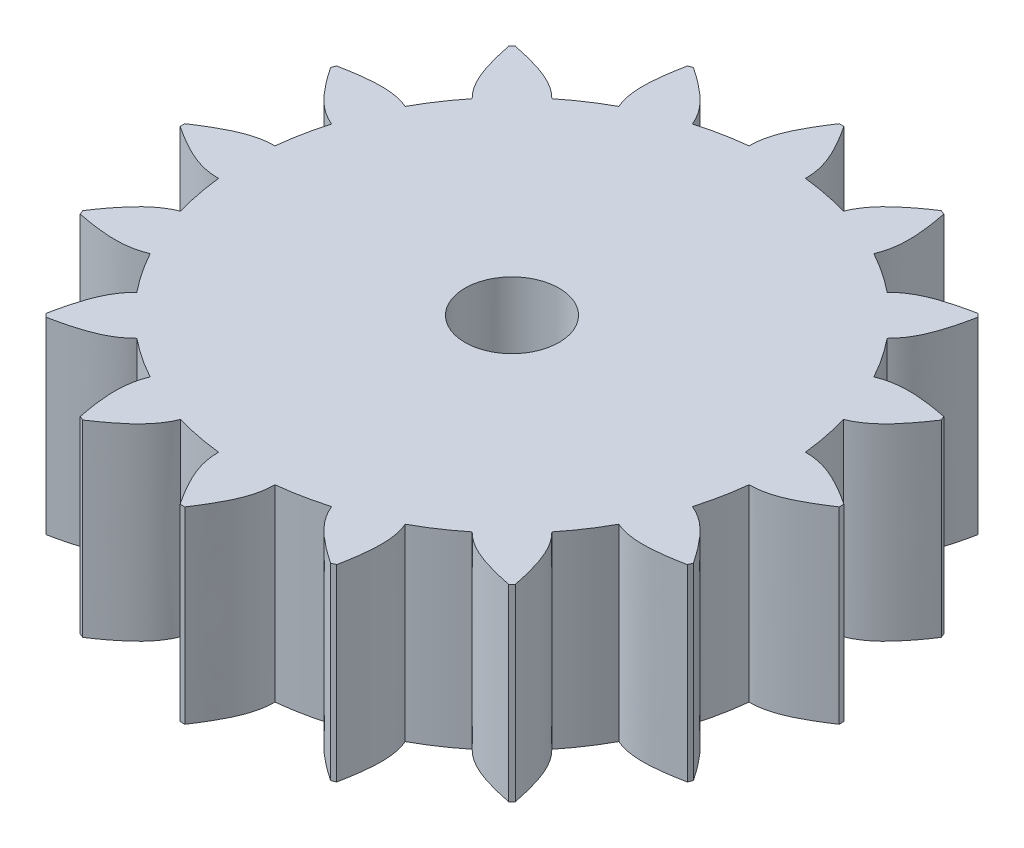
SolidWorks part; units mm, degrees
ref_plane "Front Plane" through (0, 0, 0) normal (0, 0, 1) x (1, 0, 0)
ref_plane "Top Plane" through (0, 0, 0) normal (0, 1, 0) x (1, 0, 0)
ref_plane "Right Plane" through (0, 0, 0) normal (1, 0, 0) x (0, 0, -1)
sketch "Sketch1" plane through (0, 0, 0) normal (0, 1, 0) x (1, 0, 0)
  line L0 (0, 0) -> (0, 10.795) construction
  line L1 (0, 0) -> (-1.3932, 10.7047) construction
  line L2 (0, 0) -> (1.3931, 10.7047) construction
  line L3 (0, 0) -> (4.0866, 9.9916) construction
  line L4 (0, 0) -> (6.5079, 8.6128) construction
  line L10 (1.3931, 10.7047) -> (-1.3776, 11.0653) construction
  line L11 (4.0866, 9.9916) -> (-1.0855, 12.107) construction
  line L12 (6.5079, 8.6128) -> (-0.1797, 13.6659) construction
  circle A0 centre (0, 0) radius 13.335
  circle A1 centre (0, 0) radius 10.795
  spline S0 degree 3 poles (-1.3932, 10.7047) (-1.4212, 11.7939) (-0.7474, 12.8124) (-0.1797, 13.6659) knots 0 0 0 0 1 1 1 1 construction
  spline S1 degree 3 poles (1.3932, 10.7047) (1.4212, 11.7939) (0.7474, 12.8124) (0.1797, 13.6659) knots 0 0 0 0 1 1 1 1 construction
  spline S2 degree 1 poles (-1.1392, 10.7113) (0.0318, 13.5253) knots 0 0 1 1 construction
  spline S3 degree 3 poles (-1.1392, 10.7113) (-1.1521, 11.2102) (-0.8543, 12.1818) (-0.2607, 13.0855) (0.0318, 13.5253) knots 0 0 0 0 0.5 1 1 1 1
  spline S4 degree 1 poles (1.1392, 10.7113) (-0.0318, 13.5253) knots 0 0 1 1 construction
  spline S5 degree 3 poles (1.1392, 10.7113) (1.1521, 11.2102) (0.8543, 12.1818) (0.2607, 13.0855) (-0.0318, 13.5253) knots 0 0 0 0 0.5 1 1 1 1
  dimension "D1" = 26.67
  dimension "D2" = 21.59
  dimension "D3" = 2.794
  dimension "D4" = 7.415
  dimension "D6" = 8.382
  dimension "D7" = 29.66
  dimension "D8" = 44.49
  dimension "D9" = 2.794
  dimension "D10" = 0.254
  dimension "D11" = 0.254
  dimension "D5" = 5.588
extrude "Boss-Extrude1" add sketch "Sketch1" along normal blind 7.62
pattern_circular "CirPattern1" count 16 over 360 about axis through (0, 7.62, 0) along (0, 1, 0) of "Boss-Extrude1"
sketch "Sketch2" plane through (0, 7.62, 0) normal (0, 1, 0) x (1, 0, 0)
  circle A0 centre (0, 0) radius 1.905
  dimension "D1" = 3.81
extrude "Cut-Extrude1" cut sketch "Sketch2" against normal through all
sketch "Sketch4" plane through (0, 0, 0) normal (0, -1, 0) x (1, 0, 0)
  circle A0 centre (0, 0) radius 3.175
  dimension "D1" = 6.35
extrude "Cut-Extrude2" cut sketch "Sketch4" against normal blind 3.81
